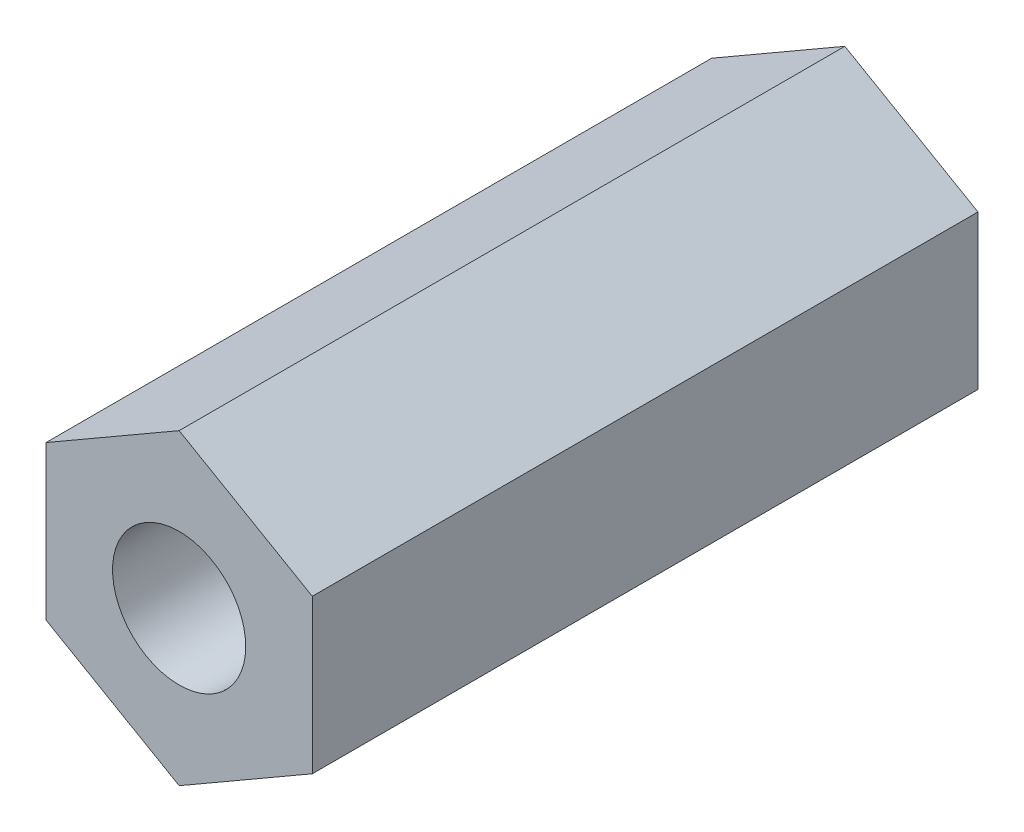
SolidWorks part; units mm, degrees
material "Bronze pour coussinet"
ref_plane "Plan de face" through (0, 0, 0) normal (0, 0, 1) x (1, 0, 0)
ref_plane "Plan de dessus" through (0, 0, 0) normal (0, 1, 0) x (1, 0, 0)
ref_plane "Plan de droite" through (0, 0, 0) normal (1, 0, 0) x (0, 0, -1)
sketch "Esquisse1" plane through (0, 0, 0) normal (0, 0, 1) x (1, 0, 0)
  line L1 (0, -3.4641) -> (3, -1.7321)
  line L2 (3, -1.7321) -> (3, 1.7321)
  line L3 (3, 1.7321) -> (0, 3.4641)
  line L4 (0, 3.4641) -> (-3, 1.7321)
  line L5 (-3, 1.7321) -> (-3, -1.7321)
  line L6 (-3, -1.7321) -> (0, -3.4641)
  circle A0 centre (0, 0) radius 3 construction
  dimension "D1" = 6
extrude "Boss.-Extru.1" add sketch "Esquisse1" along normal blind 15
sketch "Esquisse2" plane through (0, 0, 0) normal (0, 0, -1) x (-1, 0, 0)
  circle A0 centre (0, 0) radius 1.5
  dimension "D1" = 3
extrude "Enlèv. mat.-Extru.1" cut sketch "Esquisse2" against normal blind 5
sketch "Esquisse3" plane through (0, 0, 15) normal (0, 0, 1) x (1, 0, 0)
  circle A0 centre (0, 0) radius 1.5
  dimension "D1" = 3
extrude "Enlèv. mat.-Extru.2" cut sketch "Esquisse3" against normal blind 5
